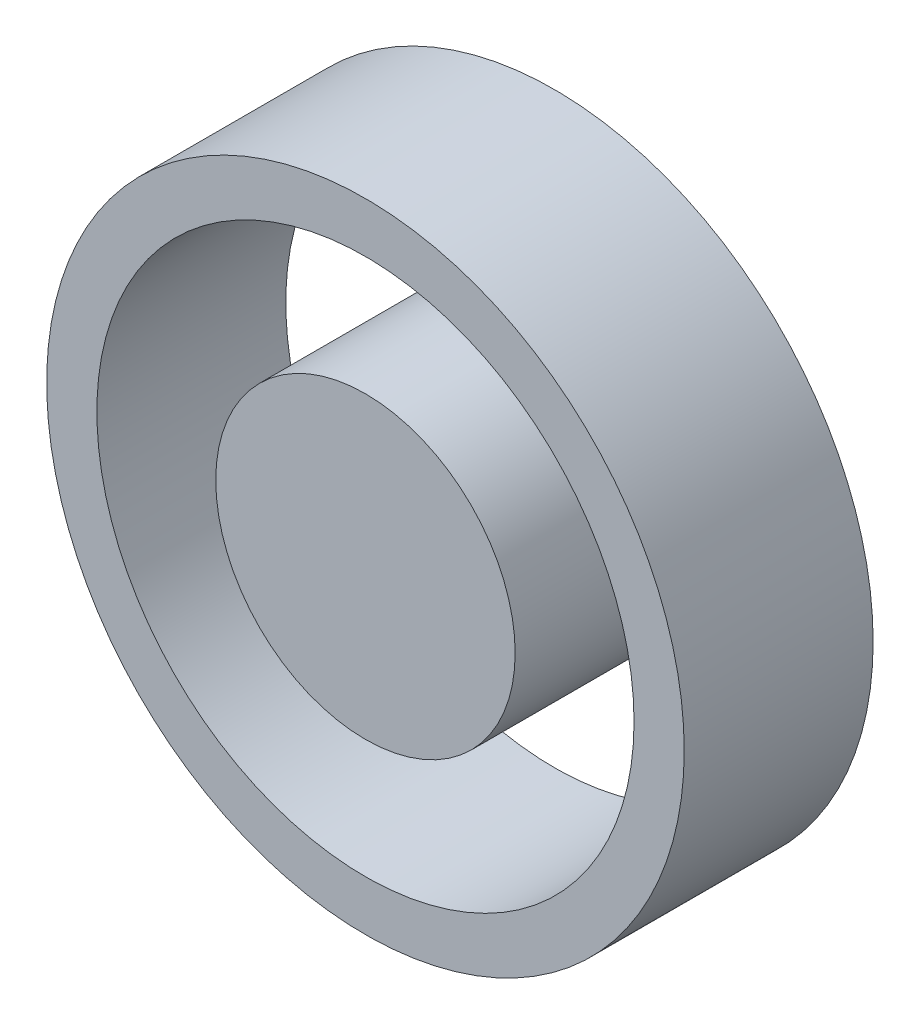
SolidWorks part; units mm, degrees
material "ABS"
ref_plane "Front Plane" through (0, 0, 0) normal (0, 0, 1) x (1, 0, 0)
ref_plane "Top Plane" through (0, 0, 0) normal (0, 1, 0) x (1, 0, 0)
ref_plane "Right Plane" through (0, 0, 0) normal (1, 0, 0) x (0, 0, -1)
sketch "Sketch1" plane through (0, 0, 0) normal (0, 0, 1) x (1, 0, 0)
  circle A0 centre (0, 0) radius 85.725
  circle A1 centre (0, 0) radius 72.2313
  circle A2 centre (0, 0) radius 40.259
  dimension "D1" = 171.45
  dimension "D2" = 144.4625
  dimension "D3" = 80.518
extrude "Boss-Extrude1" add sketch "Sketch1" along normal blind 50.8 contours A0 A1 | A2
